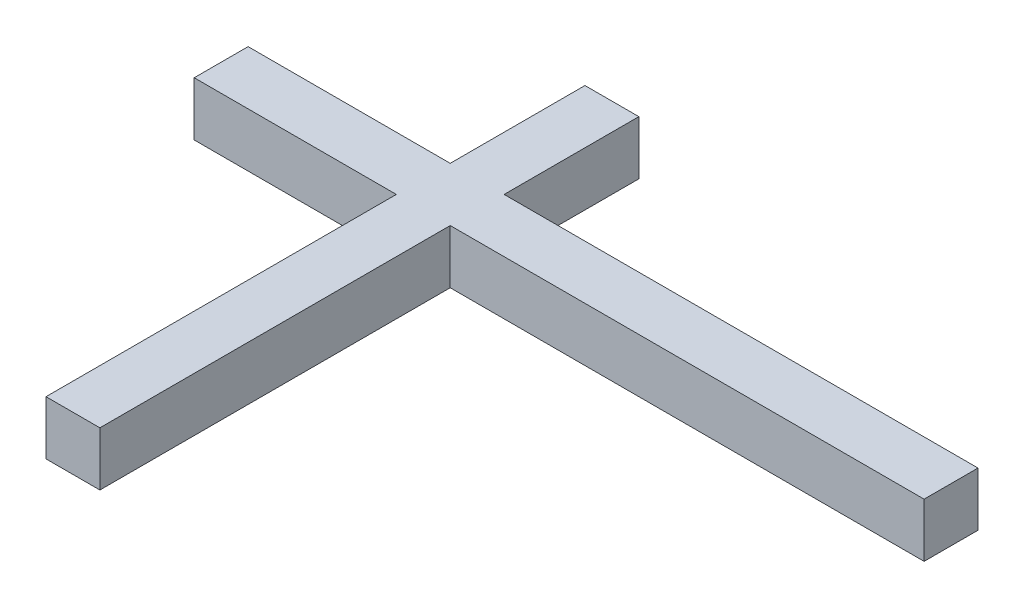
SolidWorks part; units mm, degrees
ref_plane "Front Plane" through (0, 0, 0) normal (0, 0, 1) x (1, 0, 0)
ref_plane "Top Plane" through (0, 0, 0) normal (0, 1, 0) x (1, 0, 0)
ref_plane "Right Plane" through (0, 0, 0) normal (1, 0, 0) x (0, 0, -1)
sketch "Sketch1" plane through (0, 0, 0) normal (0, 1, 0) x (1, 0, 0)
  line L0 (-9.363, -28) -> (-9.363, -80)
  line L1 (-9.363, 0) -> (-1.363, 0)
  line L2 (-9.363, 0) -> (-9.363, -20)
  line L3 (-9.363, -80) -> (-1.363, -80)
  line L4 (-1.363, 0) -> (-1.363, -20)
  line L5 (-39.363, -20) -> (-9.363, -20)
  line L6 (-39.363, -20) -> (-39.363, -28)
  line L7 (-39.363, -28) -> (-9.363, -28)
  line L8 (68.9786, -20) -> (68.9786, -28)
  line L9 (-1.363, -20) -> (68.9786, -20)
  line L10 (-1.363, -28) -> (-1.363, -80)
  line L11 (-1.363, -28) -> (68.9786, -28)
  dimension "D1" = 8
  dimension "D2" = 80
  dimension "D3" = 8
  dimension "D4" = 20
  dimension "D5" = 30
extrude "Boss-Extrude1" add sketch "Sketch1" along normal blind 8
